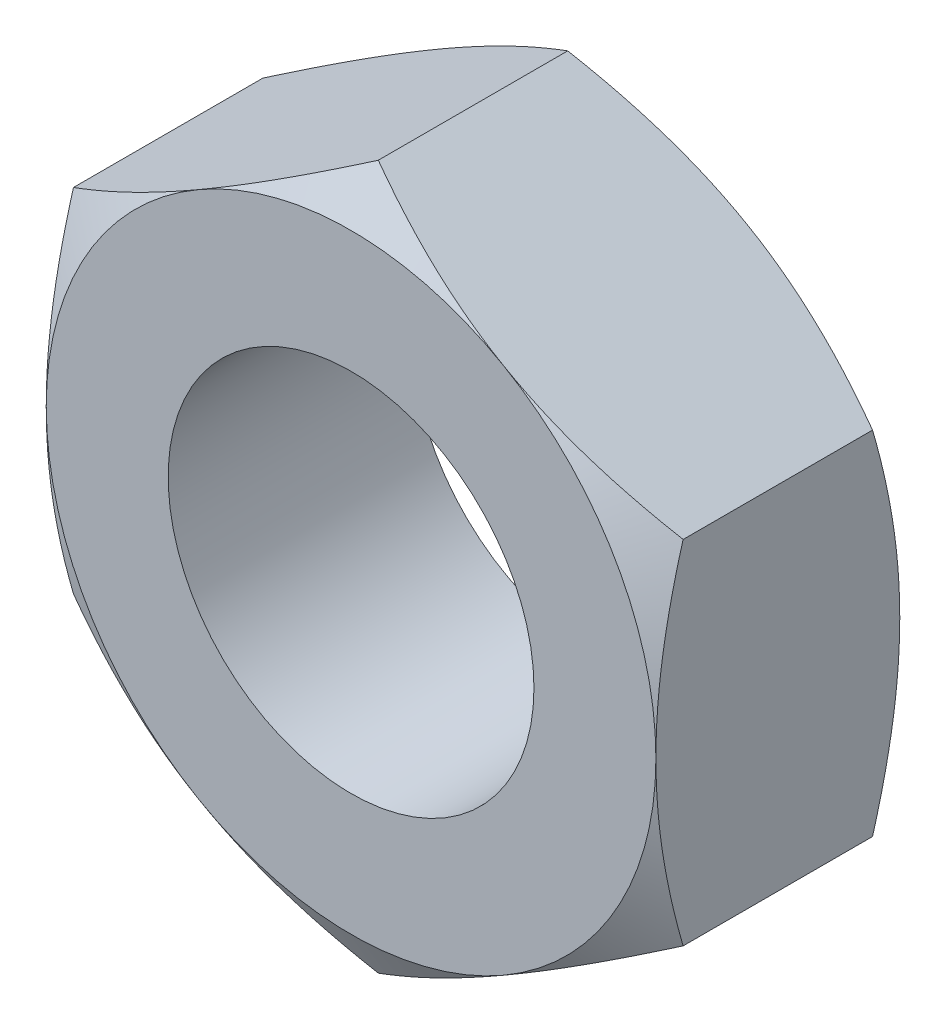
SolidWorks part; units mm, degrees
ref_plane "Front Plane" through (0, 0, 0) normal (0, 0, 1) x (1, 0, 0)
ref_plane "Top Plane" through (0, 0, 0) normal (0, 1, 0) x (1, 0, 0)
ref_plane "Right Plane" through (0, 0, 0) normal (1, 0, 0) x (0, 0, -1)
sketch "Sketch1" plane through (0, 0, 0) normal (0, 0, 1) x (1, 0, 0)
  line L1 (0, -2.8868) -> (2.5, -1.4434)
  line L2 (2.5, -1.4434) -> (2.5, 1.4434)
  line L3 (2.5, 1.4434) -> (0, 2.8868)
  line L4 (0, 2.8868) -> (-2.5, 1.4434)
  line L5 (-2.5, 1.4434) -> (-2.5, -1.4434)
  line L6 (-2.5, -1.4434) -> (0, -2.8868)
  circle A0 centre (0, 0) radius 1.5
  circle A1 centre (0, 0) radius 2.5 construction
  point P3 (0, 0)
  dimension "D1" = 5
  dimension "D2" = 3
extrude "Boss-Extrude1" add sketch "Sketch1" along normal blind 2
cosmetic thread "Cosmetic Thread1" parameters "D1"=2, "D2"=4
sketch "Sketch2" plane through (0, 0, 2) normal (0, 0, 1) x (1, 0, 0)
  circle A0 centre (0, 0) radius 2.5 construction
  circle A1 centre (0, 0) radius 2.5
extrude "Cut-Extrude1" cut sketch "Sketch2" against normal blind 2 draft 60 flip side to cut
sketch "Sketch3" plane through (0, 0, 0) normal (0, 0, -1) x (-1, 0, 0)
  circle A0 centre (0, 0) radius 2.5 construction
  circle A1 centre (0, 0) radius 2.5
extrude "Cut-Extrude2" cut sketch "Sketch3" against normal blind 2 draft 60 flip side to cut
